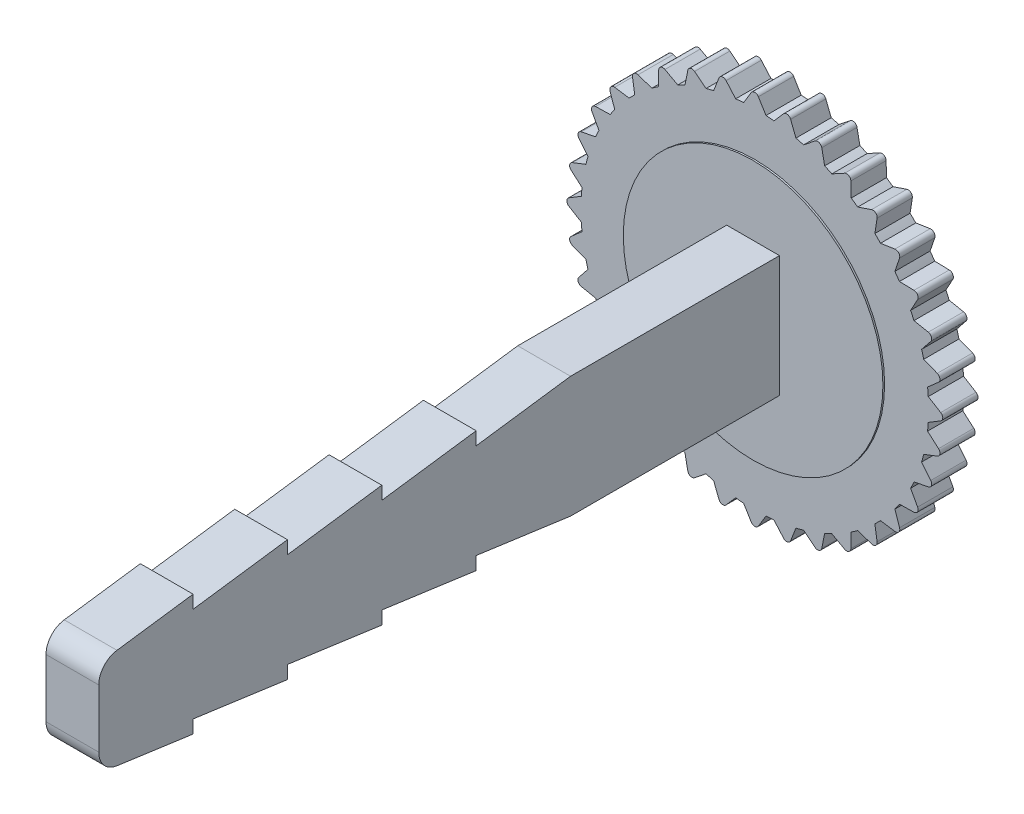
SolidWorks part; units mm, degrees
material "1060 Alloy"
ref_plane "Front Plane" through (0, 0, 0) normal (0, 0, 1) x (1, 0, 0)
ref_plane "Top Plane" through (0, 0, 0) normal (0, 1, 0) x (1, 0, 0)
ref_plane "Right Plane" through (0, 0, 0) normal (1, 0, 0) x (0, 0, -1)
sketch "Sketch1" plane through (0, 0, 0) normal (0, 0, 1) x (1, 0, 0)
  line L0 (0, 0) -> (0, 13.4429) construction
  line L1 (-0.53, 8.2179) -> (-0.1709, 8.8089)
  line L2 (0.53, 8.2179) -> (0.1709, 8.8089)
  line L5 (1.949, 8.001) -> (1.698, 8.6454)
  line L6 (0.9051, 8.1851) -> (1.3613, 8.7047)
  line L7 (3.3087, 7.5411) -> (3.1734, 8.2192)
  line L8 (2.3127, 7.9036) -> (2.8522, 8.3361)
  line L9 (4.568, 6.8519) -> (4.5524, 7.5432)
  line L10 (3.65, 7.3819) -> (4.2564, 7.7142)
  line L11 (5.6884, 5.9546) -> (5.7932, 6.6381)
  line L12 (4.8764, 6.636) -> (5.5313, 6.8578)
  line L13 (6.636, 4.8764) -> (6.8578, 5.5313)
  line L14 (5.9546, 5.6884) -> (6.6381, 5.7932)
  line L15 (7.3819, 3.65) -> (7.7142, 4.2564)
  line L16 (6.8519, 4.568) -> (7.5432, 4.5524)
  line L17 (7.9036, 2.3127) -> (8.3361, 2.8522)
  line L18 (7.5411, 3.3087) -> (8.2192, 3.1734)
  line L19 (8.1851, 0.9051) -> (8.7047, 1.3613)
  line L20 (8.001, 1.949) -> (8.6454, 1.698)
  line L21 (8.2179, -0.53) -> (8.8089, -0.1709)
  line L22 (8.2179, 0.53) -> (8.8089, 0.1709)
  line L23 (8.001, -1.949) -> (8.6454, -1.698)
  line L24 (8.1851, -0.9051) -> (8.7047, -1.3613)
  line L25 (7.5411, -3.3087) -> (8.2192, -3.1734)
  line L26 (7.9036, -2.3127) -> (8.3361, -2.8522)
  line L27 (6.8519, -4.568) -> (7.5432, -4.5524)
  line L28 (7.3819, -3.65) -> (7.7142, -4.2564)
  line L29 (5.9546, -5.6884) -> (6.6381, -5.7932)
  line L30 (6.636, -4.8764) -> (6.8578, -5.5313)
  line L31 (4.8764, -6.636) -> (5.5313, -6.8578)
  line L32 (5.6884, -5.9546) -> (5.7932, -6.6381)
  line L33 (3.65, -7.3819) -> (4.2564, -7.7142)
  line L34 (4.568, -6.8519) -> (4.5524, -7.5432)
  line L35 (2.3127, -7.9036) -> (2.8522, -8.3361)
  line L36 (3.3087, -7.5411) -> (3.1734, -8.2192)
  line L37 (0.9051, -8.1851) -> (1.3613, -8.7047)
  line L38 (1.949, -8.001) -> (1.698, -8.6454)
  line L39 (-0.53, -8.2179) -> (-0.1709, -8.8089)
  line L40 (0.53, -8.2179) -> (0.1709, -8.8089)
  line L41 (-1.949, -8.001) -> (-1.698, -8.6454)
  line L42 (-0.9051, -8.1851) -> (-1.3613, -8.7047)
  line L43 (-3.3087, -7.5411) -> (-3.1734, -8.2192)
  line L44 (-2.3127, -7.9036) -> (-2.8522, -8.3361)
  line L45 (-4.568, -6.8519) -> (-4.5524, -7.5432)
  line L46 (-3.65, -7.3819) -> (-4.2564, -7.7142)
  line L47 (-5.6884, -5.9546) -> (-5.7932, -6.6381)
  line L48 (-4.8764, -6.636) -> (-5.5313, -6.8578)
  line L49 (-6.636, -4.8764) -> (-6.8578, -5.5313)
  line L50 (-5.9546, -5.6884) -> (-6.6381, -5.7932)
  line L51 (-7.3819, -3.65) -> (-7.7142, -4.2564)
  line L52 (-6.8519, -4.568) -> (-7.5432, -4.5524)
  line L53 (-7.9036, -2.3127) -> (-8.3361, -2.8522)
  line L54 (-7.5411, -3.3087) -> (-8.2192, -3.1734)
  line L55 (-8.1851, -0.9051) -> (-8.7047, -1.3613)
  line L56 (-8.001, -1.949) -> (-8.6454, -1.698)
  line L57 (-8.2179, 0.53) -> (-8.8089, 0.1709)
  line L58 (-8.2179, -0.53) -> (-8.8089, -0.1709)
  line L59 (-8.001, 1.949) -> (-8.6454, 1.698)
  line L60 (-8.1851, 0.9051) -> (-8.7047, 1.3613)
  line L61 (-7.5411, 3.3087) -> (-8.2192, 3.1734)
  line L62 (-7.9036, 2.3127) -> (-8.3361, 2.8522)
  line L63 (-6.8519, 4.568) -> (-7.5432, 4.5524)
  line L64 (-7.3819, 3.65) -> (-7.7142, 4.2564)
  line L65 (-5.9546, 5.6884) -> (-6.6381, 5.7932)
  line L66 (-6.636, 4.8764) -> (-6.8578, 5.5313)
  line L67 (-4.8764, 6.636) -> (-5.5313, 6.8578)
  line L68 (-5.6884, 5.9546) -> (-5.7932, 6.6381)
  line L69 (-3.65, 7.3819) -> (-4.2564, 7.7142)
  line L70 (-4.568, 6.8519) -> (-4.5524, 7.5432)
  line L71 (-2.3127, 7.9036) -> (-2.8522, 8.3361)
  line L72 (-3.3087, 7.5411) -> (-3.1734, 8.2192)
  line L73 (-0.9051, 8.1851) -> (-1.3613, 8.7047)
  line L74 (-1.949, 8.001) -> (-1.698, 8.6454)
  arc A1 (-6.636, 4.8764) -> (-6.8519, 4.568) centre (0, 0) ccw
  arc A2 (0.1709, 8.8089) -> (-0.1709, 8.8089) centre (0, 8.705) ccw
  arc A3 (1.698, 8.6454) -> (1.3613, 8.7047) centre (1.5116, 8.5728) ccw
  arc A4 (3.1734, 8.2192) -> (2.8522, 8.3361) centre (2.9773, 8.18) ccw
  arc A5 (4.5524, 7.5432) -> (4.2564, 7.7142) centre (4.3525, 7.5388) ccw
  arc A6 (5.7932, 6.6381) -> (5.5313, 6.8578) centre (5.5955, 6.6684) ccw
  arc A7 (6.8578, 5.5313) -> (6.6381, 5.7932) centre (6.6684, 5.5955) ccw
  arc A8 (7.7142, 4.2564) -> (7.5432, 4.5524) centre (7.5388, 4.3525) ccw
  arc A9 (8.3361, 2.8522) -> (8.2192, 3.1734) centre (8.18, 2.9773) ccw
  arc A10 (8.7047, 1.3613) -> (8.6454, 1.698) centre (8.5728, 1.5116) ccw
  arc A11 (8.8089, -0.1709) -> (8.8089, 0.1709) centre (8.705, 0) ccw
  arc A12 (8.6454, -1.698) -> (8.7047, -1.3613) centre (8.5728, -1.5116) ccw
  arc A13 (8.2192, -3.1734) -> (8.3361, -2.8522) centre (8.18, -2.9773) ccw
  arc A14 (7.5432, -4.5524) -> (7.7142, -4.2564) centre (7.5388, -4.3525) ccw
  arc A15 (6.6381, -5.7932) -> (6.8578, -5.5313) centre (6.6684, -5.5955) ccw
  arc A16 (5.5313, -6.8578) -> (5.7932, -6.6381) centre (5.5955, -6.6684) ccw
  arc A17 (4.2564, -7.7142) -> (4.5524, -7.5432) centre (4.3525, -7.5388) ccw
  arc A18 (2.8522, -8.3361) -> (3.1734, -8.2192) centre (2.9773, -8.18) ccw
  arc A19 (1.3613, -8.7047) -> (1.698, -8.6454) centre (1.5116, -8.5728) ccw
  arc A20 (-0.1709, -8.8089) -> (0.1709, -8.8089) centre (0, -8.705) ccw
  arc A21 (-1.698, -8.6454) -> (-1.3613, -8.7047) centre (-1.5116, -8.5728) ccw
  arc A22 (-3.1734, -8.2192) -> (-2.8522, -8.3361) centre (-2.9773, -8.18) ccw
  arc A23 (-4.5524, -7.5432) -> (-4.2564, -7.7142) centre (-4.3525, -7.5388) ccw
  arc A24 (-5.7932, -6.6381) -> (-5.5313, -6.8578) centre (-5.5955, -6.6684) ccw
  arc A25 (-6.8578, -5.5313) -> (-6.6381, -5.7932) centre (-6.6684, -5.5955) ccw
  arc A26 (-7.7142, -4.2564) -> (-7.5432, -4.5524) centre (-7.5388, -4.3525) ccw
  arc A27 (-8.3361, -2.8522) -> (-8.2192, -3.1734) centre (-8.18, -2.9773) ccw
  arc A28 (-8.7047, -1.3613) -> (-8.6454, -1.698) centre (-8.5728, -1.5116) ccw
  arc A29 (-8.8089, 0.1709) -> (-8.8089, -0.1709) centre (-8.705, 0) ccw
  arc A30 (-8.6454, 1.698) -> (-8.7047, 1.3613) centre (-8.5728, 1.5116) ccw
  arc A31 (-8.2192, 3.1734) -> (-8.3361, 2.8522) centre (-8.18, 2.9773) ccw
  arc A32 (-7.5432, 4.5524) -> (-7.7142, 4.2564) centre (-7.5388, 4.3525) ccw
  arc A33 (-6.6381, 5.7932) -> (-6.8578, 5.5313) centre (-6.6684, 5.5955) ccw
  arc A34 (-5.5313, 6.8578) -> (-5.7932, 6.6381) centre (-5.5955, 6.6684) ccw
  arc A35 (-4.2564, 7.7142) -> (-4.5524, 7.5432) centre (-4.3525, 7.5388) ccw
  arc A36 (-2.8522, 8.3361) -> (-3.1734, 8.2192) centre (-2.9773, 8.18) ccw
  arc A37 (-1.3613, 8.7047) -> (-1.698, 8.6454) centre (-1.5116, 8.5728) ccw
  arc A38 (-5.6884, 5.9546) -> (-5.9546, 5.6884) centre (0, 0) ccw
  arc A39 (-4.568, 6.8519) -> (-4.8764, 6.636) centre (0, 0) ccw
  arc A40 (-3.3087, 7.5411) -> (-3.65, 7.3819) centre (0, 0) ccw
  arc A41 (-1.949, 8.001) -> (-2.3127, 7.9036) centre (0, 0) ccw
  arc A42 (-0.53, 8.2179) -> (-0.9051, 8.1851) centre (0, 0) ccw
  arc A43 (0.9051, 8.1851) -> (0.53, 8.2179) centre (0, 0) ccw
  arc A44 (2.3127, 7.9036) -> (1.949, 8.001) centre (0, 0) ccw
  arc A45 (3.65, 7.3819) -> (3.3087, 7.5411) centre (0, 0) ccw
  arc A46 (4.8764, 6.636) -> (4.568, 6.8519) centre (0, 0) ccw
  arc A47 (6.8519, 4.568) -> (6.636, 4.8764) centre (0, 0) ccw
  arc A48 (5.9546, 5.6884) -> (5.6884, 5.9546) centre (0, 0) ccw
  arc A49 (7.5411, 3.3087) -> (7.3819, 3.65) centre (0, 0) ccw
  arc A50 (8.001, 1.949) -> (7.9036, 2.3127) centre (0, 0) ccw
  arc A51 (8.2179, 0.53) -> (8.1851, 0.9051) centre (0, 0) ccw
  arc A52 (8.1851, -0.9051) -> (8.2179, -0.53) centre (0, 0) ccw
  arc A53 (7.9036, -2.3127) -> (8.001, -1.949) centre (0, 0) ccw
  arc A54 (7.3819, -3.65) -> (7.5411, -3.3087) centre (0, 0) ccw
  arc A55 (6.636, -4.8764) -> (6.8519, -4.568) centre (0, 0) ccw
  arc A56 (5.6884, -5.9546) -> (5.9546, -5.6884) centre (0, 0) ccw
  arc A57 (4.568, -6.8519) -> (4.8764, -6.636) centre (0, 0) ccw
  arc A58 (3.3087, -7.5411) -> (3.65, -7.3819) centre (0, 0) ccw
  arc A59 (1.949, -8.001) -> (2.3127, -7.9036) centre (0, 0) ccw
  arc A60 (0.53, -8.2179) -> (0.9051, -8.1851) centre (0, 0) ccw
  arc A61 (-0.9051, -8.1851) -> (-0.53, -8.2179) centre (0, 0) ccw
  arc A62 (-2.3127, -7.9036) -> (-1.949, -8.001) centre (0, 0) ccw
  arc A63 (-3.65, -7.3819) -> (-3.3087, -7.5411) centre (0, 0) ccw
  arc A64 (-4.8764, -6.636) -> (-4.568, -6.8519) centre (0, 0) ccw
  arc A65 (-5.9546, -5.6884) -> (-5.6884, -5.9546) centre (0, 0) ccw
  arc A66 (-6.8519, -4.568) -> (-6.636, -4.8764) centre (0, 0) ccw
  arc A67 (-7.5411, -3.3087) -> (-7.3819, -3.65) centre (0, 0) ccw
  arc A68 (-8.001, -1.949) -> (-7.9036, -2.3127) centre (0, 0) ccw
  arc A69 (-8.2179, -0.53) -> (-8.1851, -0.9051) centre (0, 0) ccw
  arc A70 (-7.3819, 3.65) -> (-7.5411, 3.3087) centre (0, 0) ccw
  arc A71 (-7.9036, 2.3127) -> (-8.001, 1.949) centre (0, 0) ccw
  arc A72 (-8.1851, 0.9051) -> (-8.2179, 0.53) centre (0, 0) ccw
  point P190 (0, 0)
  dimension "D2" = 16.47
  dimension "D5" = 0.2
  dimension "D3" = 1.06
  dimension "D4" = 1.06
  dimension "D6" = 36
extrude "Boss-Extrude1" add sketch "Sketch1" along normal blind 1.67
sketch "Sketch2" plane through (0, 0, 1.67) normal (0, 0, 1) x (1, 0, 0)
  line L1 (-1.25, 2.87) -> (1.25, 2.87)
  line L2 (-1.25, 2.87) -> (-1.25, -2.87)
  line L3 (-1.25, -2.87) -> (1.25, -2.87)
  line L4 (1.25, 2.87) -> (1.25, -2.87)
  point P4 (-1.25, 0)
  point P6 (0, -2.87)
  dimension "D1" = 2.5
  dimension "D2" = 5.74
extrude "Boss-Extrude8" add sketch "Sketch2" along normal offset from surface (32.33 mm away) 34 contours L2 L1 L4 L3 up to face at (0, 0, 0)
sketch "Sketch3" plane through (1.25, 0, 0) normal (1, 0, 0) x (0, 0, -1)
  line L0 (-1.67, 2.87) -> (-11.65, 2.87)
  line L1 (-34, 2.87) -> (-1.67, 2.87) construction
  line L2 (-11.65, 2.87) -> (-16.12, 2.25)
  line L3 (-16.12, 2.25) -> (-16.12, 2.87)
  line L4 (-16.12, 2.87) -> (-20.59, 2.25)
  line L5 (-1.67, 0) -> (-34, 0) construction
  line L6 (-1.67, -2.87) -> (-1.67, 2.87) construction
  line L7 (-34, -2.87) -> (-34, 2.87) construction
  line L8 (-29.53, -2.87) -> (-34, -2.25)
  line L9 (-29.53, -2.25) -> (-29.53, -2.87)
  line L10 (-25.06, -2.87) -> (-29.53, -2.25)
  line L11 (-20.59, 2.25) -> (-20.59, 2.87)
  line L12 (-20.59, 2.87) -> (-25.06, 2.25)
  line L13 (-25.06, 2.25) -> (-25.06, 2.87)
  line L14 (-25.06, 2.87) -> (-29.53, 2.25)
  line L15 (-29.53, 2.25) -> (-29.53, 2.87)
  line L16 (-29.53, 2.87) -> (-34, 2.25)
  line L17 (-34, 2.25) -> (-34, -2.25)
  line L18 (-25.06, -2.25) -> (-25.06, -2.87)
  line L19 (-20.59, -2.87) -> (-25.06, -2.25)
  line L20 (-20.59, -2.25) -> (-20.59, -2.87)
  line L21 (-16.12, -2.87) -> (-20.59, -2.25)
  line L22 (-16.12, -2.25) -> (-16.12, -2.87)
  line L23 (-11.65, -2.87) -> (-16.12, -2.25)
  line L24 (-1.67, -2.87) -> (-11.65, -2.87)
  line L25 (-34, 2.25) -> (-34, 2.87)
  line L26 (-34, 2.87) -> (-11.65, 2.87)
  line L27 (-34, -2.25) -> (-34, -2.87)
  line L28 (-34, -2.87) -> (-11.65, -2.87)
  line M24 (-34, 2.87) -> (-34, -2.87)
  line M25 (-34, -2.87) -> (-1.67, -2.87)
  line M27 (-1.67, 2.87) -> (-34, 2.87)
  dimension "D2" = 4.47
  dimension "D3" = 4.47
  dimension "D5" = 4.47
  dimension "D6" = 4.47
  dimension "D7" = 4.47
extrude "Cut-Extrude1" cut sketch "Sketch3" against normal blind 34 contours L8 M25 M24 | L10 L9 M25 | L19 L18 M25 | L21 L20 M25 | L23 L22 M25 | L3 L2 M27 | L11 L4 M27 | L13 L12 M27 | L15 L14 M27 | L16 M27 M24
fillet "Fillet1" radius 1 2 edges at (0, 2.25, 34) (0, -2.25, 34)
sketch "Sketch4" plane through (0, 0, 0) normal (0, 0, -1) x (-1, 0, 0)
  circle A0 centre (0, 0) radius 6.15
  dimension "D1" = 12.3
extrude "Cut-Extrude2" cut sketch "Sketch4" against normal blind 0.08
sketch "Sketch5" plane through (0, 0, 1.67) normal (0, 0, 1) x (1, 0, 0)
  circle A0 centre (0, 0) radius 6.15
  dimension "D1" = 12.3
extrude "Boss-Extrude9" add sketch "Sketch5" along normal blind 0.08
sketch "Sketch6" plane through (0, 0, 0.08) normal (0, 0, -1) x (-1, 0, 0)
  circle A0 centre (0, 0) radius 2.5
  dimension "D1" = 5
extrude "Boss-Extrude10" add sketch "Sketch6" along normal blind 0.19
